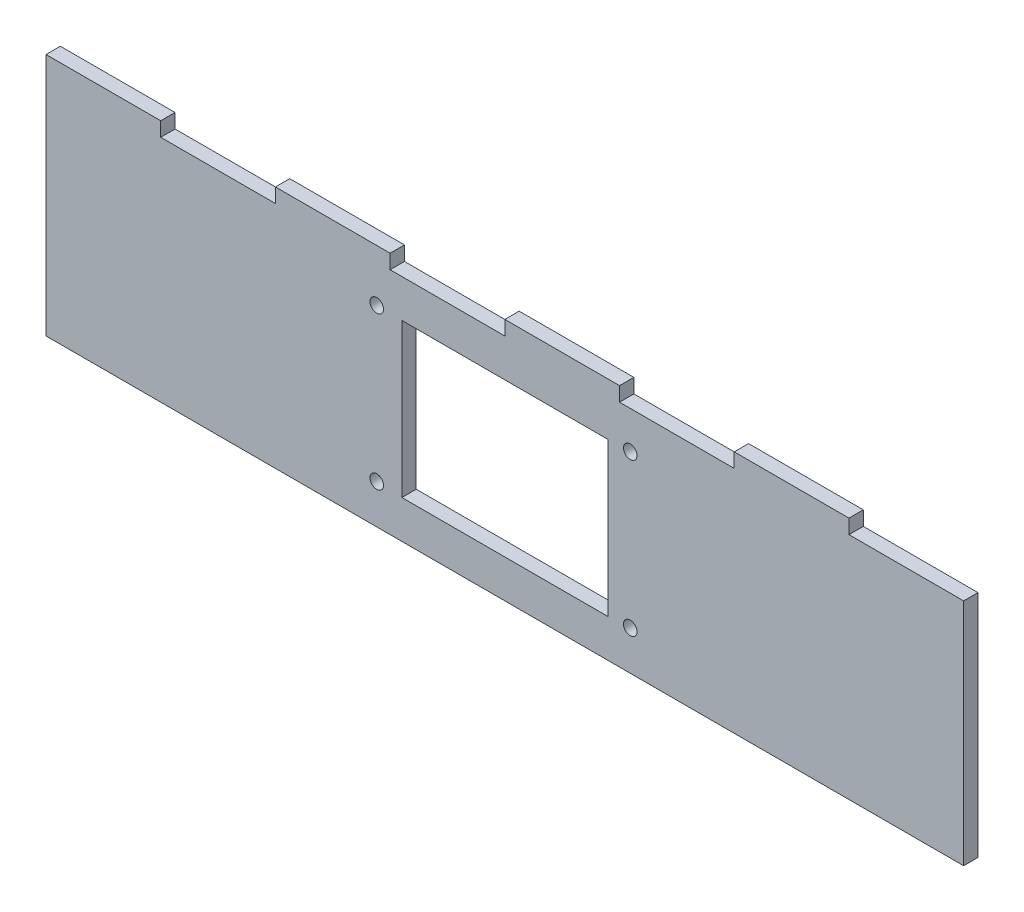
SolidWorks part; units mm, degrees
ref_plane "Front Plane" through (0, 0, 0) normal (0, 0, 1) x (1, 0, 0)
ref_plane "Top Plane" through (0, 0, 0) normal (0, 1, 0) x (1, 0, 0)
ref_plane "Right Plane" through (0, 0, 0) normal (1, 0, 0) x (0, 0, -1)
sketch "Sketch1" plane through (0, 0, 0) normal (0, 0, 1) x (1, 0, 0)
  line L1 (-101.6, -25.4) -> (101.6, -25.4)
  line L2 (-101.6, -25.4) -> (-101.6, 25.4)
  line L3 (-101.6, 25.4) -> (101.6, 25.4)
  line L4 (101.6, -25.4) -> (101.6, 25.4)
  line L5 (-101.6, -25.4) -> (101.6, 25.4) construction
  line L6 (-101.6, 25.4) -> (101.6, -25.4) construction
  point P0 (0, 0)
  dimension "D1" = 203.2
  dimension "D2" = 50.8
extrude "Boss-Extrude1" add sketch "Sketch1" along normal blind 3.175
sketch "Sketch2" plane through (0, 0, 3.175) normal (0, 0, 1) x (1, 0, 0)
  line L1 (-22.8, -16.98) -> (22.8, -16.98)
  line L2 (-22.8, -16.98) -> (-22.8, 16.98)
  line L3 (-22.8, 16.98) -> (22.8, 16.98)
  line L4 (22.8, -16.98) -> (22.8, 16.98)
  line L5 (-22.8, -16.98) -> (22.8, 16.98) construction
  line L6 (-22.8, 16.98) -> (22.8, -16.98) construction
  circle A0 centre (27.7691, 17.0828) radius 1.5
  circle A1 centre (-28.3649, 17.0828) radius 1.5
  circle A2 centre (-28.3649, -16.6992) radius 1.5
  circle A3 centre (27.7691, -16.6992) radius 1.5
  point P0 (0, 0)
  dimension "D5" = 3
  dimension "D1" = 45.6
  dimension "D2" = 33.96
  dimension "D3" = 2
  dimension "D4" = 2
extrude "Cut-Extrude1" cut sketch "Sketch2" against normal blind 3.175
sketch "Sketch3" plane through (0, 0, 3.175) normal (0, 0, 1) x (1, 0, 0)
  line L0 (-50.8, 25.4) -> (-50.8, 28.575)
  line L1 (-101.6, 25.4) -> (-76.2, 25.4)
  line L2 (-101.6, 25.4) -> (-101.6, 28.575)
  line L3 (-101.6, 28.575) -> (-76.2, 28.575)
  line L4 (-76.2, 25.4) -> (-76.2, 28.575)
  line L5 (-50.8, 25.4) -> (-25.4, 25.4)
  line L6 (-25.4, 25.4) -> (-25.4, 28.575)
  line L7 (-50.8, 28.575) -> (-25.4, 28.575)
  line L8 (0, 25.4) -> (0, 28.575)
  line L9 (0, 25.4) -> (25.4, 25.4)
  line L10 (25.4, 25.4) -> (25.4, 28.575)
  line L11 (0, 28.575) -> (25.4, 28.575)
  line L12 (50.8, 25.4) -> (50.8, 28.575)
  line L13 (50.8, 25.4) -> (76.2, 25.4)
  line L14 (76.2, 25.4) -> (76.2, 28.575)
  line L15 (50.8, 28.575) -> (76.2, 28.575)
  dimension "D1" = 3.175
  dimension "D2" = 25.4
  dimension "D3" = 4
extrude "Boss-Extrude2" add sketch "Sketch3" against normal blind 3.175
